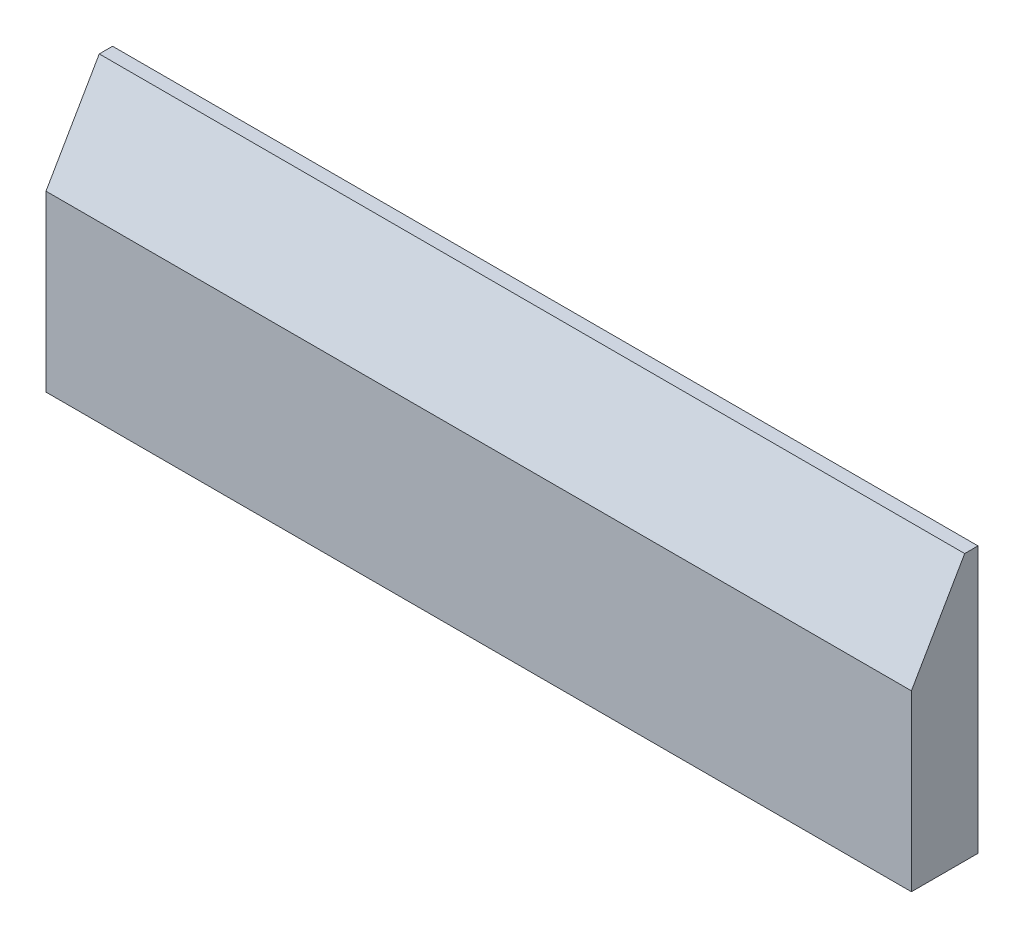
SolidWorks part; units mm, degrees
ref_plane "Front Plane" through (0, 0, 0) normal (0, 0, 1) x (1, 0, 0)
ref_plane "Top Plane" through (0, 0, 0) normal (0, 1, 0) x (1, 0, 0)
ref_plane "Right Plane" through (0, 0, 0) normal (1, 0, 0) x (0, 0, -1)
sketch "Sketch1" plane through (0, 0, 0) normal (0, 0, 1) x (1, 0, 0)
  line L1 (0, 0) -> (82.55, 0)
  line L2 (0, 0) -> (0, 25.4)
  line L3 (0, 25.4) -> (82.55, 25.4)
  line L4 (82.55, 0) -> (82.55, 25.4)
  dimension "D1" = 82.55
  dimension "D2" = 25.4
extrude "Boss-Extrude1" add sketch "Sketch1" along normal blind 6.35
chamfer "Chamfer1" distance 5.08 angle 60 1 edges at (41.275, 25.4, 6.35)
